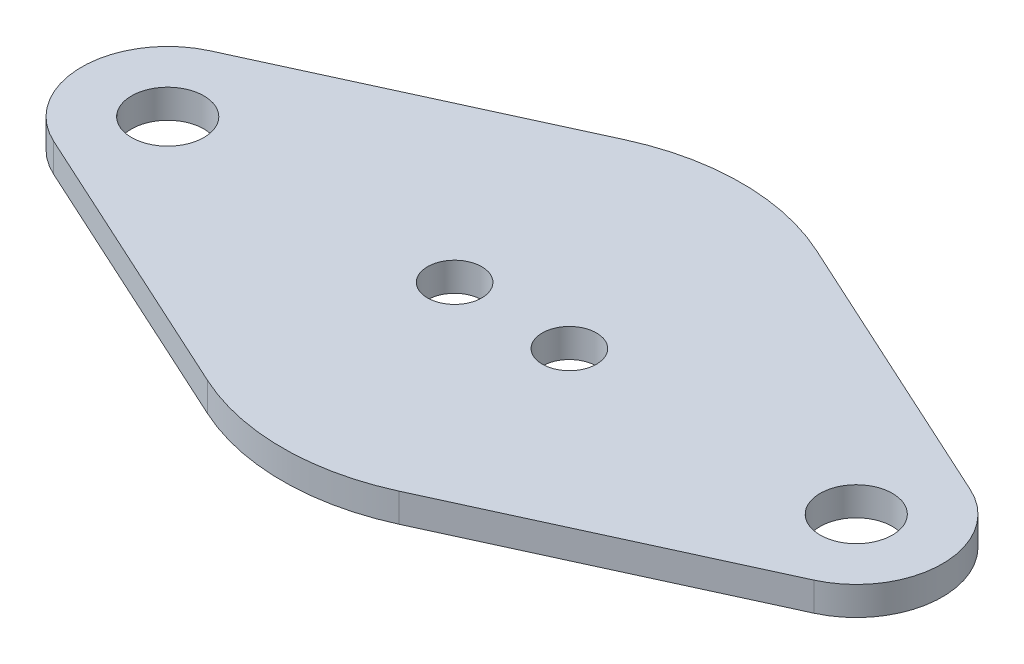
SolidWorks part; units mm, degrees
ref_plane "Front Plane" through (0, 0, 0) normal (0, 0, 1) x (1, 0, 0)
ref_plane "Top Plane" through (0, 0, 0) normal (0, 1, 0) x (1, 0, 0)
ref_plane "Right Plane" through (0, 0, 0) normal (1, 0, 0) x (0, 0, -1)
sketch "Sketch1" plane through (0, 0, 0) normal (0, 1, 0) x (1, 0, 0)
  line L0 (-42.0687, 8.6588) -> (-10.5833, 23.0901)
  line L1 (10.5833, 23.0901) -> (42.0688, 8.6588)
  line L2 (42.0688, -8.6588) -> (10.5833, -23.0901)
  line L3 (-10.5833, -23.0901) -> (-42.0688, -8.6588)
  circle A0 centre (-38.1, 0) radius 4
  circle A1 centre (38.1, 0) radius 4
  arc A2 (-42.0687, 8.6588) -> (-42.0688, -8.6588) centre (-38.1, 0) ccw
  arc A3 (42.0688, -8.6588) -> (42.0688, 8.6588) centre (38.1, 0) ccw
  arc A4 (-10.5833, -23.0901) -> (10.5833, -23.0901) centre (0, 0) ccw
  arc A5 (10.5833, 23.0901) -> (-10.5833, 23.0901) centre (0, 0) ccw
  circle A6 centre (6.35, 0) radius 3
  circle A7 centre (-6.35, 0) radius 3
  point P0 (-38.1, 0)
  point P1 (38.1, 0)
  point P6 (6.35, 0)
  point P7 (-6.35, 0)
extrude "Boss-Extrude1" add sketch "Sketch1" against normal blind 3.175
